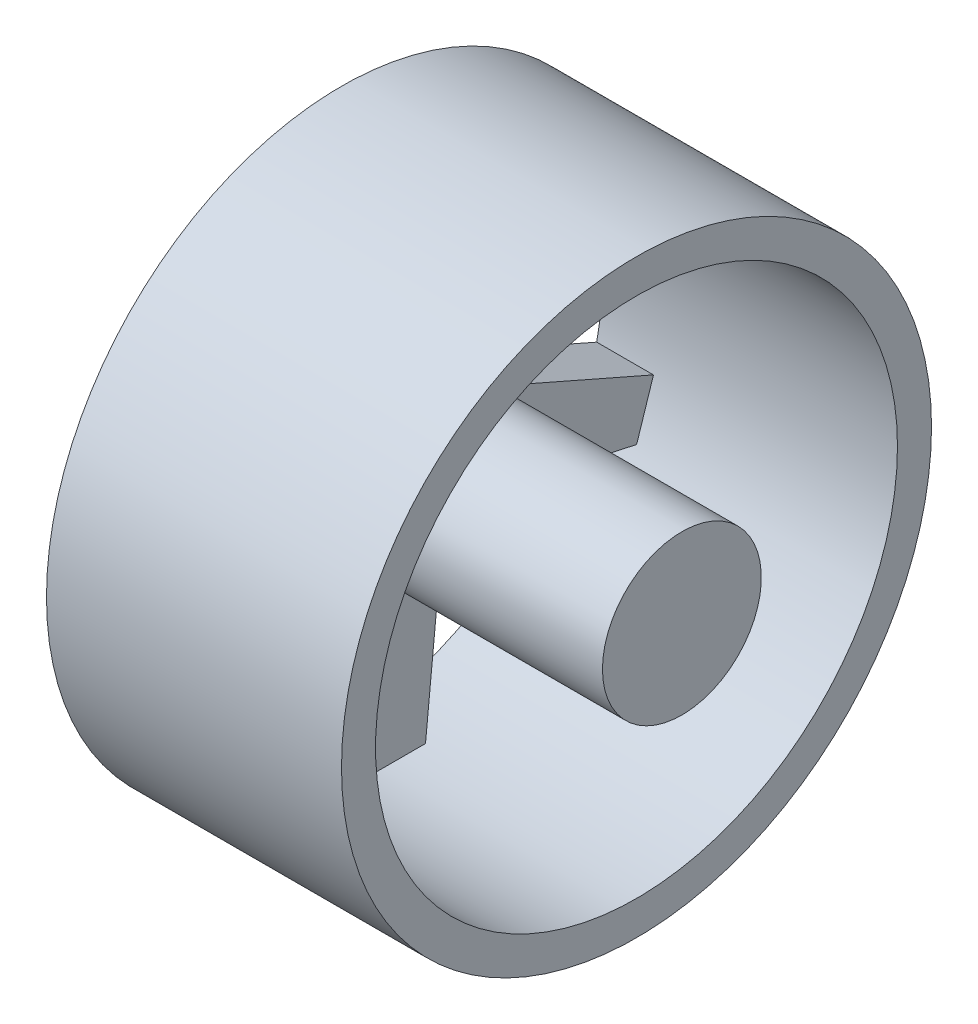
SolidWorks part; units mm, degrees
material "ABS"
ref_plane "Спереди" through (0, 0, 0) normal (0, 0, 1) x (1, 0, 0)
ref_plane "Сверху" through (0, 0, 0) normal (0, 1, 0) x (1, 0, 0)
ref_plane "Справа" through (0, 0, 0) normal (1, 0, 0) x (0, 0, -1)
sketch "Эскиз2" plane through (0, 0, 0) normal (1, 0, 0) x (0, 0, -1)
  circle A0 centre (0, 0) radius 23
  dimension "D1" = 46
extrude "Вытянуть-Тонкостенный1" add sketch "Эскиз2" along normal blind 26 thin
sketch "Эскиз4" plane through (0, 0, 0) normal (-1, 0, 0) x (0, 0, 1)
  circle A0 centre (0, 0) radius 7
  dimension "D1" = 14
extrude "Бобышка-Вытянуть1" add sketch "Эскиз4" against normal blind 30 separate body
sketch "Эскиз6" plane through (0, 0, 0) normal (-1, 0, 0) x (0, 0, 1)
  line L0 (0, 26) -> (0, -26) construction
  line L1 (-26, 0) -> (26, 0) construction
  line L2 (0, 7) -> (11.5, 19.9186)
  line L3 (0, 7) -> (-6.6574, 2.1631) construction
  line L4 (-6.6574, 2.1631) -> (-4.1145, -5.6631) construction
  line L5 (-4.1145, -5.6631) -> (4.1145, -5.6631) construction
  line L6 (4.1145, -5.6631) -> (6.6574, 2.1631) construction
  line L7 (6.6574, 2.1631) -> (0, 7) construction
  line L8 (2.4042, 22.874) -> (-2.4042, 22.874)
  line L9 (-2.4042, 22.874) -> (-7.1074, 21.8743)
  line L10 (-7.1074, 21.8743) -> (-11.5, 19.9186)
  line L11 (-11.5, 19.9186) -> (-15.39, 17.0923)
  line L12 (-15.39, 17.0923) -> (-18.6074, 13.5191)
  line L13 (-18.6074, 13.5191) -> (-21.0115, 9.3549)
  line L14 (-21.0115, 9.3549) -> (-22.4974, 4.782)
  line L15 (-22.4974, 4.782) -> (-23, 0)
  line L16 (-23, 0) -> (-22.4974, -4.782)
  line L17 (-22.4974, -4.782) -> (-21.0115, -9.3549)
  line L18 (-21.0115, -9.3549) -> (-18.6074, -13.5191)
  line L19 (-18.6074, -13.5191) -> (-15.39, -17.0923)
  line L20 (-15.39, -17.0923) -> (-11.5, -19.9186)
  line L21 (-11.5, -19.9186) -> (-7.1074, -21.8743)
  line L22 (-7.1074, -21.8743) -> (-2.4042, -22.874)
  line L23 (-2.4042, -22.874) -> (2.4042, -22.874)
  line L24 (2.4042, -22.874) -> (7.1074, -21.8743)
  line L25 (7.1074, -21.8743) -> (11.5, -19.9186)
  line L26 (11.5, -19.9186) -> (15.39, -17.0923)
  line L27 (15.39, -17.0923) -> (18.6074, -13.5191)
  line L28 (18.6074, -13.5191) -> (21.0115, -9.3549)
  line L29 (21.0115, -9.3549) -> (22.4974, -4.782)
  line L30 (22.4974, -4.782) -> (23, 0)
  line L31 (23, 0) -> (22.4974, 4.782)
  line L32 (22.4974, 4.782) -> (21.0115, 9.3549)
  line L33 (21.0115, 9.3549) -> (18.6074, 13.5191)
  line L34 (18.6074, 13.5191) -> (15.39, 17.0923)
  line L35 (15.39, 17.0923) -> (11.5, 19.9186)
  line L36 (11.5, 19.9186) -> (7.1074, 21.8743)
  line L37 (7.1074, 21.8743) -> (2.4042, 22.874)
  line L38 (6.6574, 2.1631) -> (15.39, 17.0923)
  line L39 (-6.6574, 2.1631) -> (-15.39, 17.0923)
  line L40 (0, 7) -> (-11.5, 19.9186)
  line L41 (-6.6574, 2.1631) -> (-22.4974, -4.782)
  line L42 (-4.1145, -5.6631) -> (-21.0115, -9.3549)
  line L43 (-4.1145, -5.6631) -> (-2.4042, -22.874)
  line L44 (4.1145, -5.6631) -> (2.4042, -22.874)
  line L45 (6.6574, 2.1631) -> (22.4974, -4.782)
  line L46 (4.1145, -5.6631) -> (21.0115, -9.3549)
  circle A0 centre (0, 0) radius 26 construction
  circle A1 centre (0, 0) radius 7 construction
  circle A2 centre (0, 0) radius 7 construction
  circle A3 centre (0, 0) radius 23 construction
  circle A4 centre (0, 0) radius 23 construction
  circle M3 centre (0, 0) radius 7
extrude "Бобышка-Вытянуть2" add sketch "Эскиз6" against normal blind 5 contours L40 L11 L39 M3 | L38 L35 L2 M3 | L46 L29 L45 M3 | L44 L43 L23 M3 | L42 L41 L17 M3
sketch "Эскиз7" plane through (0, 0, 0) normal (-1, 0, 0) x (0, 0, 1)
  circle A0 centre (0, 0) radius 6.5
  dimension "D1" = 13
extrude "Вырез-Вытянуть1" cut sketch "Эскиз7" against normal blind 3
